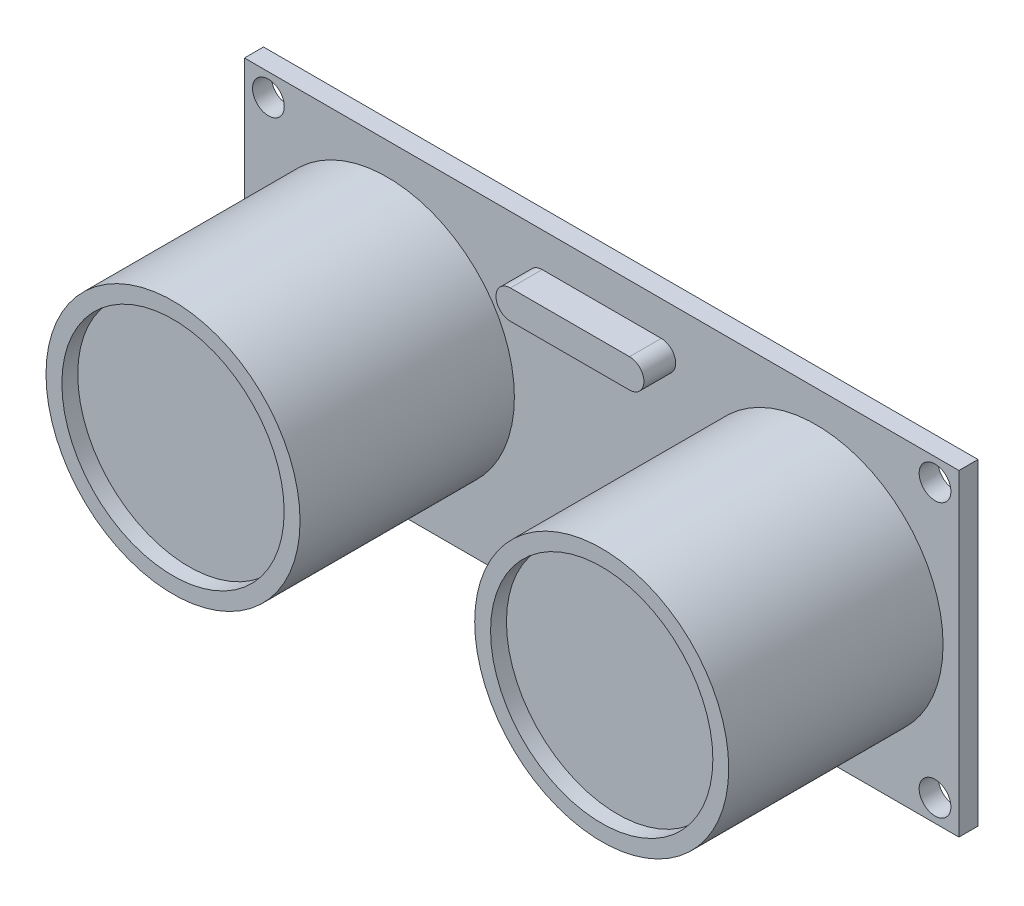
SolidWorks part; units mm, degrees
ref_plane "Front Plane" through (0, 0, 0) normal (0, 0, 1) x (1, 0, 0)
ref_plane "Top Plane" through (0, 0, 0) normal (0, 1, 0) x (1, 0, 0)
ref_plane "Right Plane" through (0, 0, 0) normal (1, 0, 0) x (0, 0, -1)
sketch "Sketch1" plane through (0, 0, 0) normal (0, 0, 1) x (1, 0, 0)
  line L0 (-13.5, 0) -> (13.5, 0) construction
  line L1 (-22.5, -10) -> (22.5, -10)
  line L2 (-22.5, -10) -> (-22.5, 10)
  line L3 (-22.5, 10) -> (22.5, 10)
  line L4 (22.5, -10) -> (22.5, 10)
  line L5 (-22.5, -10) -> (22.5, 10) construction
  line L6 (-22.5, 10) -> (22.5, -10) construction
  line L7 (0, -55) -> (0, 55) construction
  line L8 (0, 24.362) -> (0, -23.7336) construction
  circle A4 centre (-20.9935, 8.6) radius 1
  circle A5 centre (-20.9935, -8.6) radius 1
  circle A6 centre (20.9935, -8.6) radius 1
  circle A7 centre (20.9935, 8.6) radius 1
  point P0 (0, 0)
  point P9 (0, 0)
  dimension "D8" = 2
  dimension "D9" = 2
  dimension "D1" = 45
  dimension "D2" = 20
  dimension "D3" = 27
  dimension "D6" = 17.2
  dimension "D7" = 1.4
extrude "Boss-Extrude3" add sketch "Sketch1" along normal blind 1.2
sketch "Sketch5" plane through (0, 0, 1.2) normal (0, 0, 1) x (1, 0, 0)
  line L1 (0, -55) -> (0, 55) construction
  circle A0 centre (-13.5, 0) radius 8
  circle A2 centre (13.5, 0) radius 8
  dimension "D2" = 16
  dimension "D1" = 27
extrude "Extrude-Thin1" add sketch "Sketch5" along normal blind 13.5 separate body thin thin type one direction reverse wall 1
sketch "Sketch8" plane through (0, 0, 1.2) normal (0, 0, 1) x (1, 0, 0)
  line L0 (0, 0) -> (0, 13.8447) construction
  line L1 (-3.75, 6.9224) -> (3.75, 6.9224) construction
  line L2 (-3.75, 7.8316) -> (3.75, 7.8316)
  line L3 (-3.75, 6.0131) -> (3.75, 6.0131)
  arc A0 (-3.75, 7.8316) -> (-3.75, 6.0131) centre (-3.75, 6.9224) ccw
  arc A1 (3.75, 6.0131) -> (3.75, 7.8316) centre (3.75, 6.9224) ccw
  point P5 (0, 6.9224)
  dimension "D1" = 7.5
extrude "Boss-Extrude4" add sketch "Sketch8" along normal blind 2
sketch "Sketch11" plane through (0, 0, 1.2) normal (0, 0, 1) x (1, 0, 0)
  line L0 (-13.5, 7) -> (-13.5, -7) construction
  line L1 (-20.5, 0) -> (23.3251, 0) construction
  line L2 (0, -8.085) -> (0, 8.085) construction
  circle A0 centre (-13.5, 0) radius 7 construction
  circle A1 centre (-13.5, 0) radius 7
  circle A2 centre (13.5, 0) radius 7
extrude "Boss-Extrude5" add sketch "Sketch11" along normal blind 12.5
sketch "Sketch12" plane through (0, 0, 0) normal (0, 0, -1) x (-1, 0, 0)
  line L0 (0, 13.711) -> (0, -12.4967) construction
  line L1 (2.04, -8.7809) -> (1, -8.7809)
  line L2 (-2.04, -7.7409) -> (-1, -7.7409)
  line L3 (-2.04, -7.7409) -> (-2.04, -8.7809)
  line L4 (-2.04, -8.7809) -> (-1, -8.7809)
  line L5 (-1, -7.7409) -> (-1, -8.7809)
  line L6 (-2.04, -7.7409) -> (-1, -8.7809) construction
  line L7 (-2.04, -8.7809) -> (-1, -7.7409) construction
  line L8 (-5.08, -7.7409) -> (-4.04, -7.7409)
  line L9 (-5.08, -7.7409) -> (-5.08, -8.7809)
  line L10 (-5.08, -8.7809) -> (-4.04, -8.7809)
  line L11 (-4.04, -7.7409) -> (-4.04, -8.7809)
  line L12 (-5.08, -7.7409) -> (-4.04, -8.7809) construction
  line L13 (-5.08, -8.7809) -> (-4.04, -7.7409) construction
  line L14 (1, -7.7409) -> (1, -8.7809)
  line L15 (2.04, -7.7409) -> (1, -7.7409)
  line L16 (2.04, -7.7409) -> (2.04, -8.7809)
  line L17 (2.04, -8.7809) -> (1, -7.7409) construction
  line L18 (5.08, -8.7809) -> (4.04, -8.7809)
  line L19 (4.04, -7.7409) -> (4.04, -8.7809)
  line L20 (5.08, -7.7409) -> (4.04, -7.7409)
  line L21 (5.08, -7.7409) -> (5.08, -8.7809)
  line L22 (5.08, -8.7809) -> (4.04, -7.7409) construction
  line L23 (5.08, -7.7409) -> (4.04, -8.7809) construction
  point P3 (-1.52, -8.2609)
  point P8 (-4.56, -8.2609)
  point P21 (4.56, -8.2609)
  point P22 (1, -8.2609)
  point P23 (2.04, -8.2609)
  dimension "D1" = 2
  dimension "D2" = 2
extrude "Boss-Extrude6" add sketch "Sketch12" along normal blind 1
sketch "Sketch16" plane through (0, -8.7809, 0) normal (0, -1, 0) x (1, 0, 0)
  line L1 (-4.8059, -0.1699) -> (-4.2707, -0.1699)
  line L2 (-4.8059, -0.1699) -> (-4.8059, -0.705)
  line L3 (-4.8059, -0.705) -> (-4.2707, -0.705)
  line L4 (-4.2707, -0.1699) -> (-4.2707, -0.705)
  line L5 (-1.7376, -0.2257) -> (-1.2024, -0.2257)
  line L6 (-1.7376, -0.2257) -> (-1.7376, -0.7609)
  line L7 (-1.7376, -0.7609) -> (-1.2024, -0.7609)
  line L8 (-1.2024, -0.2257) -> (-1.2024, -0.7609)
  line L9 (1.2891, -0.2145) -> (1.8243, -0.2145)
  line L10 (1.2891, -0.2145) -> (1.2891, -0.7497)
  line L11 (1.2891, -0.7497) -> (1.8243, -0.7497)
  line L12 (1.8243, -0.2145) -> (1.8243, -0.7497)
  line L13 (4.2988, -0.1922) -> (4.834, -0.1922)
  line L14 (4.2988, -0.1922) -> (4.2988, -0.7274)
  line L15 (4.2988, -0.7274) -> (4.834, -0.7274)
  line L16 (4.834, -0.1922) -> (4.834, -0.7274)
extrude "Boss-Extrude7" add sketch "Sketch16" along normal blind 2
